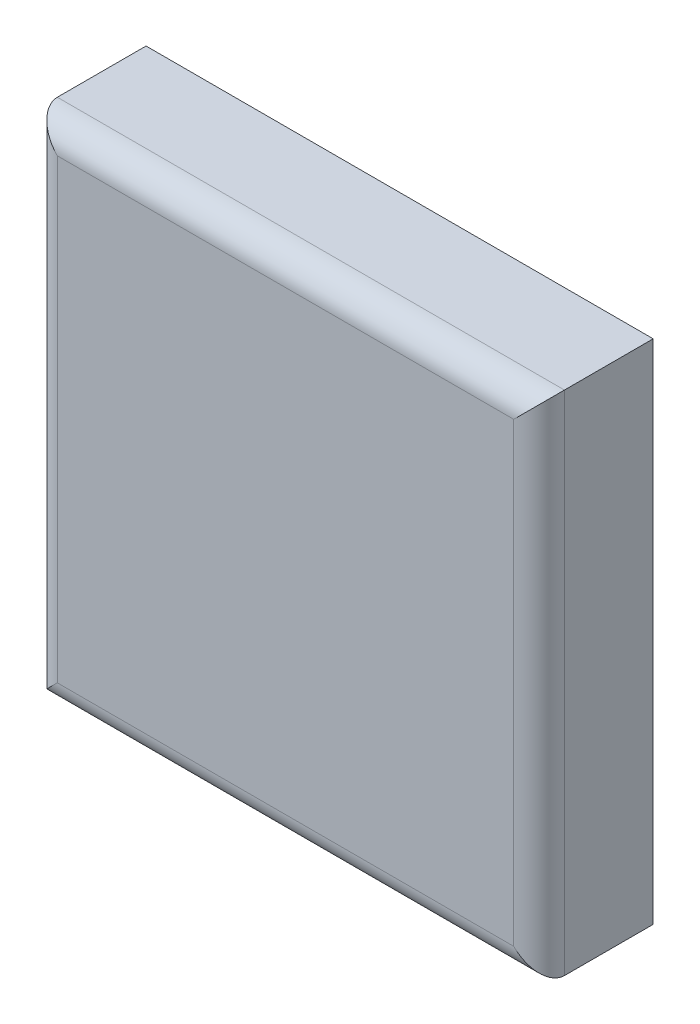
SolidWorks part; units mm, degrees
ref_plane "Front Plane" through (0, 0, 0) normal (0, 0, 1) x (1, 0, 0)
ref_plane "Top Plane" through (0, 0, 0) normal (0, 1, 0) x (1, 0, 0)
ref_plane "Right Plane" through (0, 0, 0) normal (1, 0, 0) x (0, 0, -1)
sketch "Sketch1" plane through (0, 0, 0) normal (1, 0, 0) x (0, 0, -1)
  line L0 (873.9068, 808.1653) -> (873.9068, 608.1653) construction
  line L1 (828.9068, 608.1653) -> (873.9068, 608.1653) construction
  line L2 (828.9068, 808.1653) -> (828.9068, 608.1653) construction
  line L3 (828.9068, 808.1653) -> (873.9068, 808.1653) construction
  line L4 (873.9068, 808.1653) -> (873.9068, 608.1653)
  line L5 (828.9068, 608.1653) -> (873.9068, 608.1653)
  line L6 (828.9068, 808.1653) -> (828.9068, 608.1653)
  line L7 (828.9068, 808.1653) -> (873.9068, 808.1653)
extrude "Boss-Extrude1" add sketch "Sketch1" along normal mid plane 200
fillet "Fillet1" radius 10 4 edges at (0, 808.1653, -828.9068) (100, 708.1653, -828.9068) (0, 608.1653, -828.9068) (-100, 708.1653, -828.9068)
